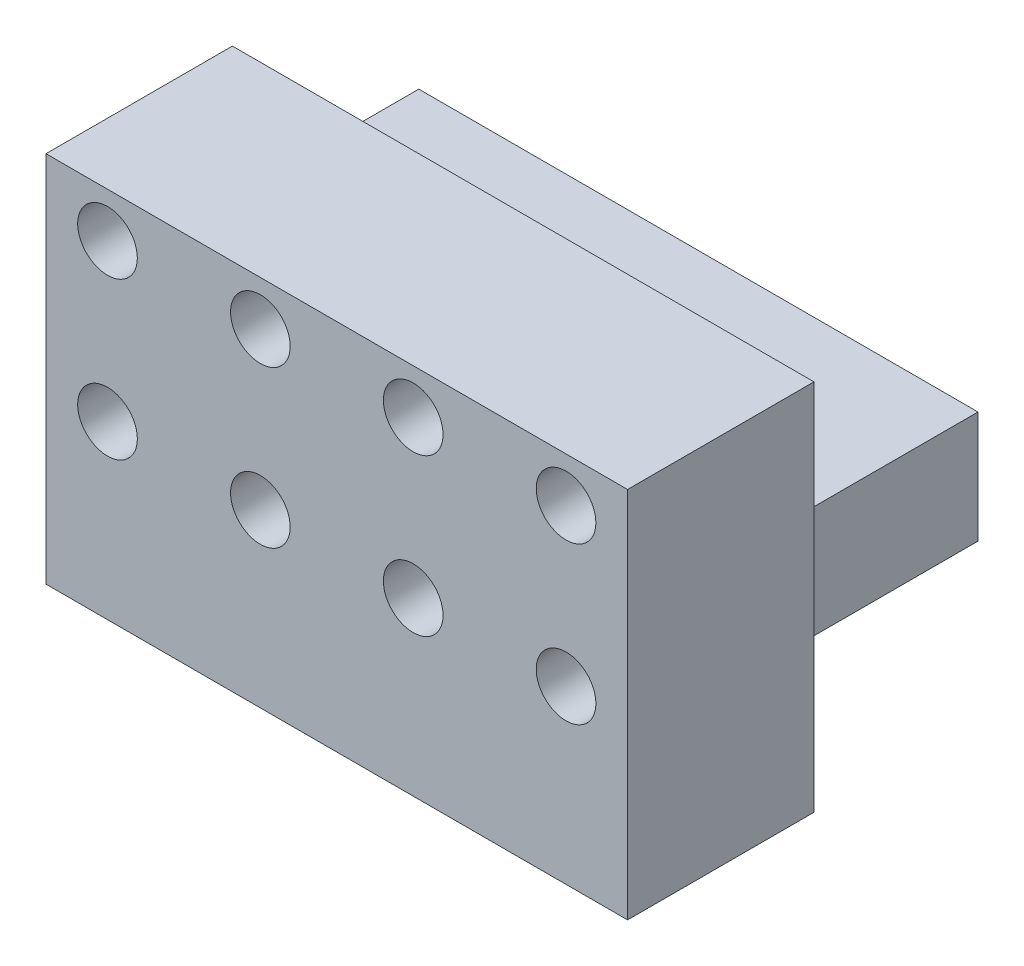
SolidWorks part; units mm, degrees
ref_plane "Front Plane" through (0, 0, 0) normal (0, 0, 1) x (1, 0, 0)
ref_plane "Top Plane" through (0, 0, 0) normal (0, 1, 0) x (1, 0, 0)
ref_plane "Right Plane" through (0, 0, 0) normal (1, 0, 0) x (0, 0, -1)
sketch "Sketch1" plane through (0, 0, 0) normal (0, 0, 1) x (1, 0, 0)
  line L0 (0, 0) -> (-38.1, 0)
  line L1 (-38.1, 0) -> (-38.1, 7.62)
  line L2 (-38.1, 7.62) -> (0, 7.62)
  line L3 (0, 7.62) -> (0, 0)
  dimension "D1" = 7.62
  dimension "D2" = 38.1
extrude "Boss-Extrude1" add sketch "Sketch1" along normal blind 12.7
sketch "Sketch2" plane through (0, 0, 12.7) normal (0, 0, 1) x (1, 0, 0)
  line L0 (-38.1, 7.62) -> (-38.1, 0) construction
  line L1 (-38.1, 16.51) -> (1.524, 16.51)
  line L2 (-38.1, 16.51) -> (-38.1, -8.89)
  line L3 (-38.1, -8.89) -> (1.524, -8.89)
  line L4 (1.524, 16.51) -> (1.524, -8.89)
  line L5 (-38.1, 16.51) -> (1.524, -8.89) construction
  line L6 (-38.1, -8.89) -> (1.524, 16.51) construction
  line L7 (0, 7.62) -> (-38.1, 7.62) construction
  point P0 (-18.288, 3.81)
  point P7 (-38.1, 3.81)
  dimension "D1" = 39.624
  dimension "D2" = 0
  dimension "D3" = 25.4
  dimension "D4" = 3.81
extrude "Boss-Extrude2" add sketch "Sketch2" along normal blind 12.7
sketch "Sketch3" plane through (0, 0, 25.4) normal (0, 0, 1) x (1, 0, 0)
  line L0 (1.524, 16.51) -> (-38.1, 16.51) construction
  line L3 (-38.1, 16.51) -> (-38.1, -8.89) construction
  circle A0 centre (-33.909, 13.462) radius 2.032
  circle A1 centre (-23.495, 13.462) radius 2.032
  circle A2 centre (-2.667, 13.462) radius 2.032
  circle A3 centre (-13.081, 2.794) radius 2.032
  circle A4 centre (-23.495, 2.794) radius 2.032
  circle A5 centre (-33.909, 2.794) radius 2.032
  circle A6 centre (-13.081, 13.462) radius 2.032
  circle A7 centre (-2.667, 2.794) radius 2.032
  point P14 (0, 0)
  dimension "D1" = 4.064
  dimension "D8" = 4.064
  dimension "D9" = 3.048
  dimension "D6" = 4.064
  dimension "D2" = 3.048
  dimension "D3" = 3.048
  dimension "D4" = 3.048
  dimension "D5" = 10.414
  dimension "D7" = 10.414
  dimension "D10" = 10.414
  dimension "D11" = 10.668
  dimension "D12" = 10.668
  dimension "D13" = 10.668
  dimension "D14" = 10.668
  dimension "D15" = 4.191
extrude "Cut-Extrude1" cut sketch "Sketch3" against normal blind 7.62
